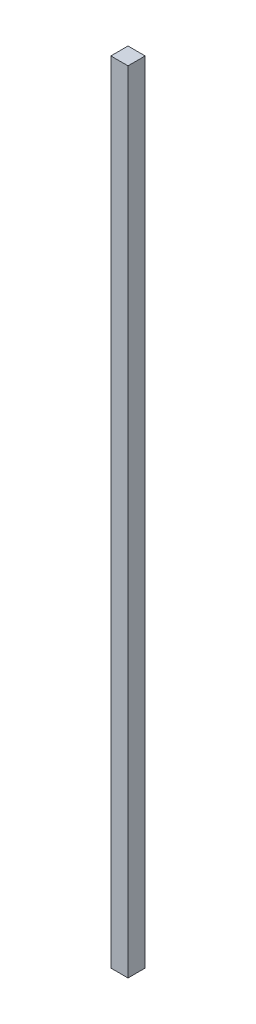
SolidWorks part; units mm, degrees
ref_plane "Plan de face" through (0, 0, 0) normal (0, 0, 1) x (1, 0, 0)
ref_plane "Plan de dessus" through (0, 0, 0) normal (0, 1, 0) x (1, 0, 0)
ref_plane "Plan de droite" through (0, 0, 0) normal (1, 0, 0) x (0, 0, -1)
sketch "Esquisse1" plane through (0, 0, 0) normal (0, 0, 1) x (1, 0, 0)
  line L1 (-40.4476, 31.9643) -> (-30.4476, 31.9643)
  line L2 (-40.4476, 31.9643) -> (-40.4476, -428.0357)
  line L3 (-40.4476, -428.0357) -> (-30.4476, -428.0357)
  line L4 (-30.4476, 31.9643) -> (-30.4476, -428.0357)
  dimension "D1" = 10
  dimension "D2" = 460
extrude "Boss.-Extru.1" add sketch "Esquisse1" along normal blind 10
equation "\"D2@Esquisse1\" = \"ProfondeurBoite\""
equation "\"EpaisseurPlaque\"= 3"
equation "\"ProfondeurBoite\"=460"
equation "\"LongueurSyphon\"=270"
equation "\"LargeurSyphon\"=120"
equation "\"HauteurCoteDroit\"= 490"
equation "\"HauteurCoteGauche\"= 540"
equation "\"HauteurSolSyphon\"= 300"
equation "\"HauteurSyphon\"=\"HauteurCoteGauche\"-\"HauteurSolSyphon\""
equation "\"LargeurDroite\"=10"
equation "\"LargeurGauche\"=150"
equation "\"LargeurBoite\"= \"LargeurDroite\" + \"LargeurGauche\" + \"LargeurSyphon\""
